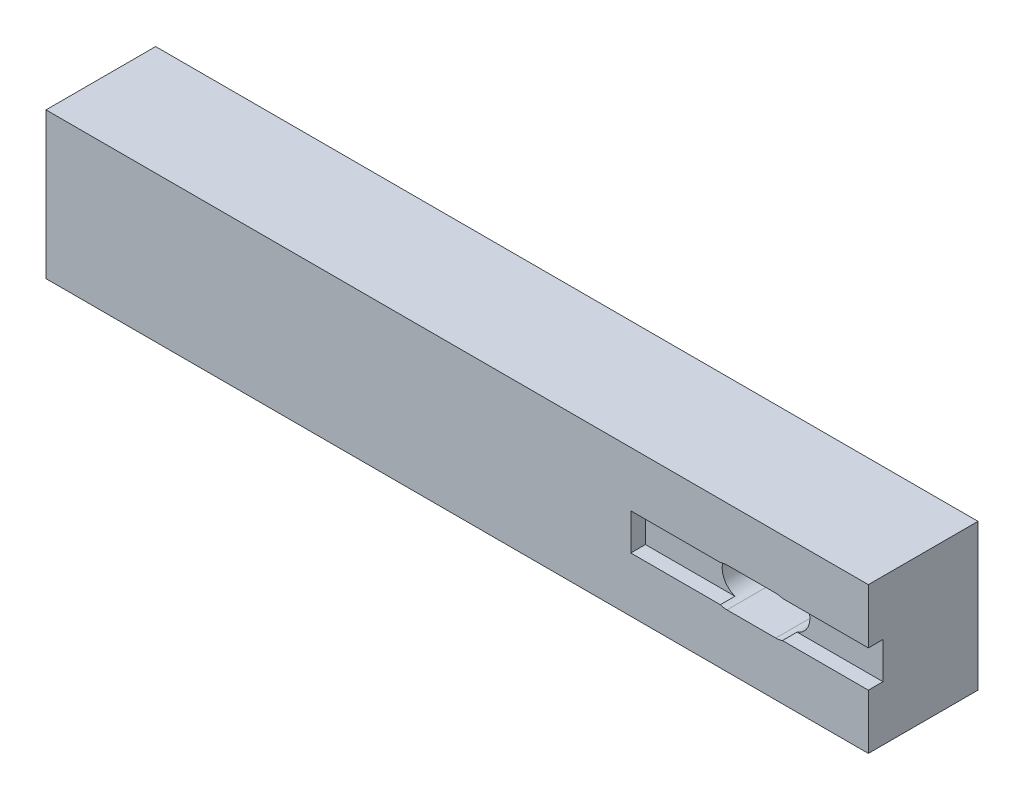
SolidWorks part; units mm, degrees
ref_plane "Front Plane" through (0, 0, 0) normal (0, 0, 1) x (1, 0, 0)
ref_plane "Top Plane" through (0, 0, 0) normal (0, 1, 0) x (1, 0, 0)
ref_plane "Right Plane" through (0, 0, 0) normal (1, 0, 0) x (0, 0, -1)
sketch "Sketch1" plane through (0, 0, 0) normal (0, 0, 1) x (1, 0, 0)
  line L0 (0, 0) -> (80, 0) construction
  line L1 (0, 13) -> (24.634, 13)
  line L2 (0, 13) -> (0, 0)
  line L3 (0, 0) -> (24.634, 0)
  line L4 (24.634, 13) -> (24.634, 0)
  line L5 (5.067, 6.5) -> (0, 6.5) construction
  line L6 (24.634, 6.5) -> (19.567, 6.5) construction
extrude "Boss-Extrude1" add sketch "Sketch1" along normal blind 10
sketch "Sketch4" plane through (0, 0, 10) normal (0, 0, 1) x (1, 0, 0)
  line L0 (24.634, 13) -> (0, 13) construction
  line L1 (0, 0) -> (82.5, 0)
  line L2 (0, 0) -> (0, 13)
  line L3 (0, 13) -> (82.5, 13)
  line L4 (82.5, 0) -> (82.5, 13)
  line L5 (80, 0) -> (80, 13) construction
  dimension "D1" = 2.5
extrude "Boss-Extrude4" add sketch "Sketch4" along normal blind 15
sketch "Sketch5" plane through (0, 0, 25) normal (0, 0, 1) x (1, 0, 0)
  line L0 (82.5, 0) -> (82.5, 13) construction
  line L1 (54.5, -3.5) -> (82.5, -3.5)
  line L2 (54.5, -3.5) -> (54.5, 0)
  line L3 (54.5, 16.5) -> (82.5, 16.5)
  line L4 (82.5, -3.5) -> (82.5, 0)
  line L5 (54.5, -3.5) -> (82.5, 16.5) construction
  line L6 (68.5, 0) -> (68.5, 13) construction
  line L7 (0, 0) -> (82.5, 0) construction
  line L8 (82.5, 13) -> (0, 13) construction
  line L9 (54.5, 0) -> (82.5, 0)
  line L10 (82.5, 13) -> (54.5, 13)
  line L11 (54.5, 13) -> (54.5, 16.5)
  line L12 (82.5, 13) -> (82.5, 16.5)
  point P13 (68.5, 6.5)
  point P14 (68.5, 6.5)
  dimension "D1" = 20
  dimension "D2" = 28
extrude "Boss-Extrude5" add sketch "Sketch5" against normal up to surface (15 mm away) up to face at (53.567, 6.5, 10)
sketch "Sketch6" plane through (0, 0, 25) normal (0, 0, 1) x (1, 0, 0)
  line L0 (54.5, 0) -> (54.5, 13) construction
  line L1 (63.16, 6.5) -> (69.84, 6.5) construction
  line L2 (63.16, 9.16) -> (69.84, 9.16)
  line L3 (63.16, 3.84) -> (69.84, 3.84)
  arc A0 (63.16, 9.16) -> (63.16, 3.84) centre (63.16, 6.5) ccw
  arc A1 (69.84, 3.84) -> (69.84, 9.16) centre (69.84, 6.5) ccw
  point P6 (66.5, 6.5)
  point P15 (54.5, 6.5)
  point P16 (60.5, 6.5)
  point P17 (72.5, 6.5)
  dimension "D1" = 5.32
  dimension "D2" = 6
  dimension "D3" = 12
extrude "Cut-Extrude1" cut sketch "Sketch6" against normal through all
sketch "Sketch7" plane through (0, 0, 25) normal (0, 0, 1) x (1, 0, 0)
  line L0 (50, 13) -> (50, 0) construction
  line L1 (50, 6.5) -> (82.5, 6.5) construction
  line L2 (82.5, -3.5) -> (82.5, 16.5) construction
  line L3 (66.25, 6.5) -> (66.25, 9) construction
  line L4 (50, 9) -> (82.5, 9)
  line L5 (50, 9) -> (50, 4)
  line L6 (50, 4) -> (82.5, 4)
  line L7 (82.5, 9) -> (82.5, 4)
  line L8 (66.25, 6.5) -> (66.25, 4) construction
  line L9 (0, 0) -> (54.5, 0) construction
  line L10 (54.5, 13) -> (0, 13) construction
  line L11 (54.5, 16.5) -> (54.5, 13) construction
  dimension "D1" = 5
  dimension "D2" = 4.5
extrude "Cut-Extrude2" cut sketch "Sketch7" against normal blind 2
sketch "Sketch8" plane through (24.634, 0, 0) normal (1, 0, 0) x (0, 0, -1)
  line L4 (0, 0) -> (0, 13)
  line L5 (0, 13) -> (-10, 13)
  line L6 (-10, 13) -> (-10, 0)
  line L7 (-10, 0) -> (0, 0)
  line L8 (0, 0) -> (0, 13)
  line L9 (0, 13) -> (-10, 13)
  line L10 (-10, 13) -> (-10, 0)
  line L11 (-10, 0) -> (0, 0)
  dimension "D1" = 0
extrude "Cut-Extrude3" cut sketch "Sketch8" against normal through all
sketch "Sketch9" plane through (54.5, 0, 0) normal (-1, 0, 0) x (0, 0, 1)
  line L0 (25, 16.5) -> (10, 16.5) construction
  line L1 (10, 16.5) -> (10, 13) construction
  line L2 (10, 13) -> (25, 13) construction
  line L3 (25, 13) -> (25, 16.5) construction
  line L4 (25, 0) -> (10, 0) construction
  line L5 (10, 0) -> (10, -3.5) construction
  line L6 (10, -3.5) -> (25, -3.5) construction
  line L7 (25, -3.5) -> (25, 0) construction
  line L8 (25, 16.5) -> (10, 16.5)
  line L9 (10, 16.5) -> (10, 13)
  line L10 (10, 13) -> (25, 13)
  line L11 (25, 13) -> (25, 16.5)
  line L12 (25, 0) -> (10, 0)
  line L13 (10, 0) -> (10, -3.5)
  line L14 (10, -3.5) -> (25, -3.5)
  line L15 (25, -3.5) -> (25, 0)
extrude "Boss-Extrude6" add sketch "Sketch9" along normal up to surface (54.5 mm away) up to face at (0, 6.5, 17.5)
sketch "Sketch10" plane through (0, 0, 0) normal (-1, 0, 0) x (0, 0, 1)
  line L4 (25, -3.5) -> (25, 16.5)
  line L5 (25, 16.5) -> (10, 16.5)
  line L6 (10, 16.5) -> (10, -3.5)
  line L7 (10, -3.5) -> (25, -3.5)
  line L8 (25, -3.5) -> (25, 16.5)
  line L9 (25, 16.5) -> (10, 16.5)
  line L10 (10, 16.5) -> (10, -3.5)
  line L11 (10, -3.5) -> (25, -3.5)
  dimension "D1" = 0
extrude "Boss-Extrude7" add sketch "Sketch10" along normal blind 30
